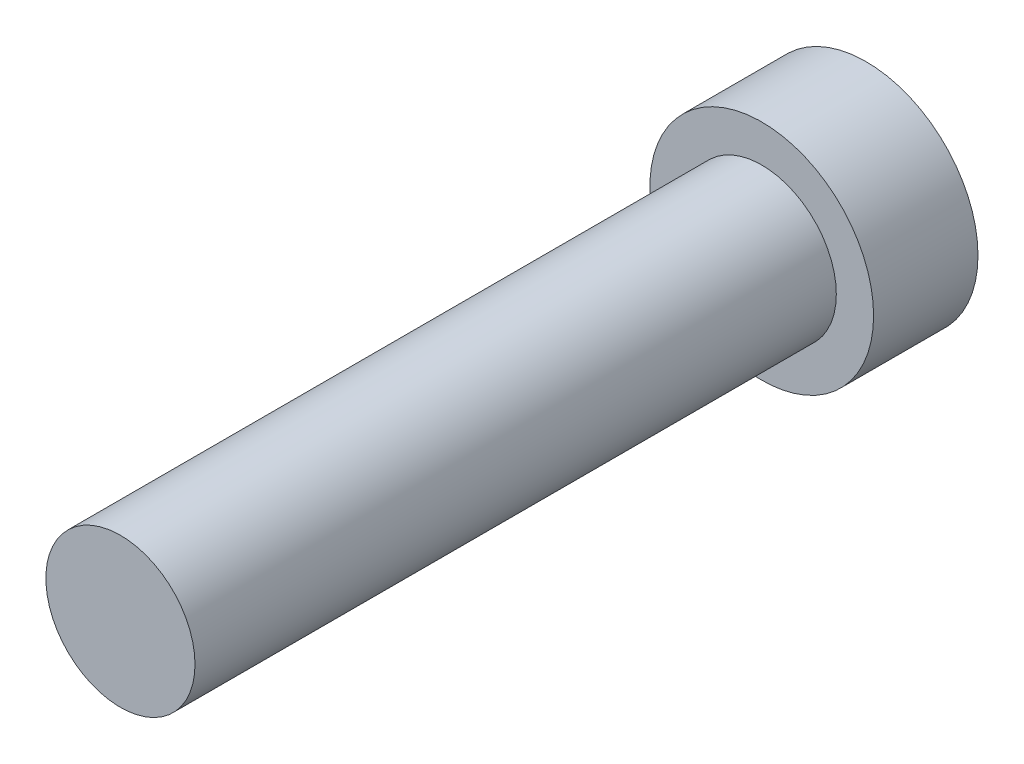
SolidWorks part; units mm, degrees
ref_plane "Front Plane" through (0, 0, 0) normal (0, 0, 1) x (1, 0, 0)
ref_plane "Top Plane" through (0, 0, 0) normal (0, 1, 0) x (1, 0, 0)
ref_plane "Right Plane" through (0, 0, 0) normal (1, 0, 0) x (0, 0, -1)
sketch "Sketch1" plane through (0, 0, 0) normal (0, 0, 1) x (1, 0, 0)
  circle A0 centre (0, 0) radius 7.5
  dimension "D1" = 15
extrude "Boss-Extrude1" add sketch "Sketch1" along normal blind 7
sketch "Sketch2" plane through (0, 0, 7) normal (0, 0, 1) x (1, 0, 0)
  circle A0 centre (0, 0) radius 5
  dimension "D1" = 10
extrude "Boss-Extrude2" add sketch "Sketch2" along normal blind 43
